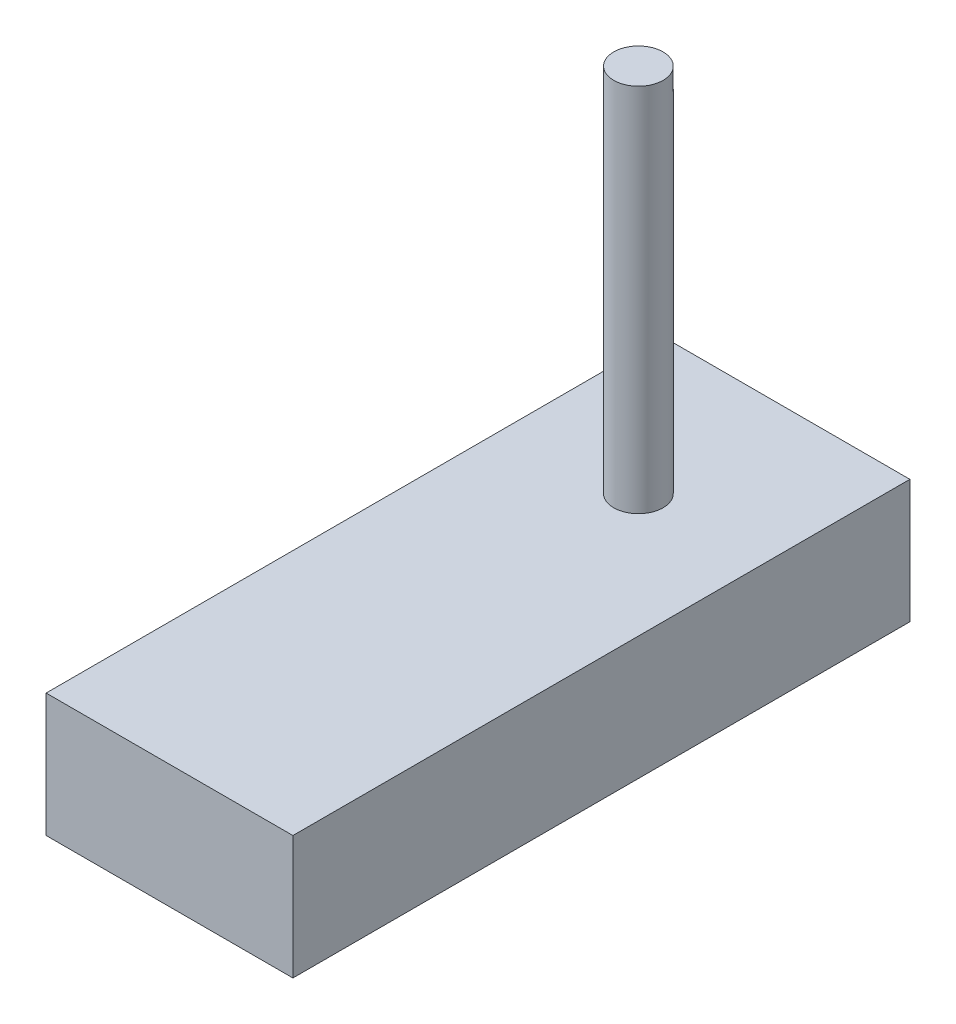
SolidWorks part; units mm, degrees
ref_plane "Alzado" through (0, 0, 0) normal (0, 0, 1) x (1, 0, 0)
ref_plane "Planta" through (0, 0, 0) normal (0, 1, 0) x (1, 0, 0)
ref_plane "Vista lateral" through (0, 0, 0) normal (1, 0, 0) x (0, 0, -1)
sketch "Croquis1" plane through (0, 0, 0) normal (0, 1, 0) x (1, 0, 0)
  line L1 (-5, -12.5) -> (5, -12.5)
  line L2 (-5, -12.5) -> (-5, 12.5)
  line L3 (-5, 12.5) -> (5, 12.5)
  line L4 (5, -12.5) -> (5, 12.5)
  line L5 (-5, -12.5) -> (5, 12.5) construction
  line L6 (-5, 12.5) -> (5, -12.5) construction
  point P0 (0, 0)
  dimension "D1" = 25
  dimension "D2" = 10
extrude "Saliente-Extruir1" add sketch "Croquis1" along normal blind 5
sketch "Croquis2" plane through (0, 5, 0) normal (0, 1, 0) x (1, 0, 0)
  line L0 (-5, -12.5) -> (5, -12.5) construction
  circle A0 centre (0, 6.5) radius 1
  dimension "D1" = 2
  dimension "D2" = 19
extrude "Saliente-Extruir2" add sketch "Croquis2" along normal blind 15
